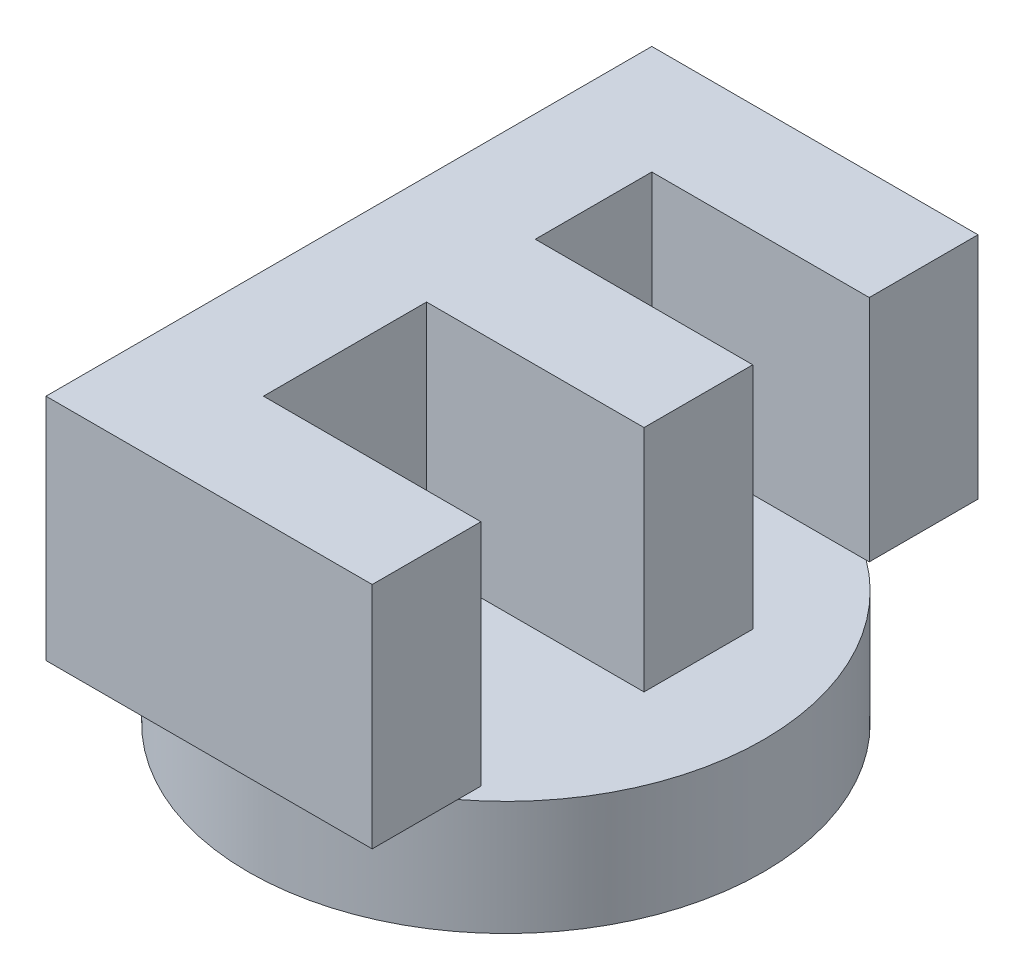
SolidWorks part; units mm, degrees
ref_plane "Front Plane" through (0, 0, 0) normal (0, 0, 1) x (1, 0, 0)
ref_plane "Top Plane" through (0, 0, 0) normal (0, 1, 0) x (1, 0, 0)
ref_plane "Right Plane" through (0, 0, 0) normal (1, 0, 0) x (0, 0, -1)
sketch "Sketch1" plane through (0, 0, 0) normal (0, 1, 0) x (1, 0, 0)
  circle A0 centre (0, 0) radius 22.5
  dimension "D1" = 45
extrude "Boss-Extrude1" add sketch "Sketch1" along normal blind 10
sketch "Sketch2" plane through (0, 10, 0) normal (0, 1, 0) x (1, 0, 0)
  text T0 "<b>E</b>" font "Century Gothic" height in points 200
extrude "Boss-Extrude2" add sketch "Sketch2" along normal blind 20
sketch "Sketch3" plane through (0, 0, 0) normal (0, -1, 0) x (1, 0, 0)
  line L0 (14.5514, 2.7786) -> (0, 30)
  line L1 (0, 30) -> (-14.5514, 2.7786)
  circle A0 centre (0, -5) radius 16.5
  circle A2 centre (0, 0) radius 22.5 construction
  circle A4 centre (0, 0) radius 21.5
  circle A5 centre (0, 0) radius 21.5
  dimension "D1" = 33
  dimension "D2" = 35
  dimension "D3" = 5
  dimension "D4" = 1
extrude "Cut-Extrude2" cut sketch "Sketch3" against normal blind 5 contours L0 A5 L1 A0 | A0
